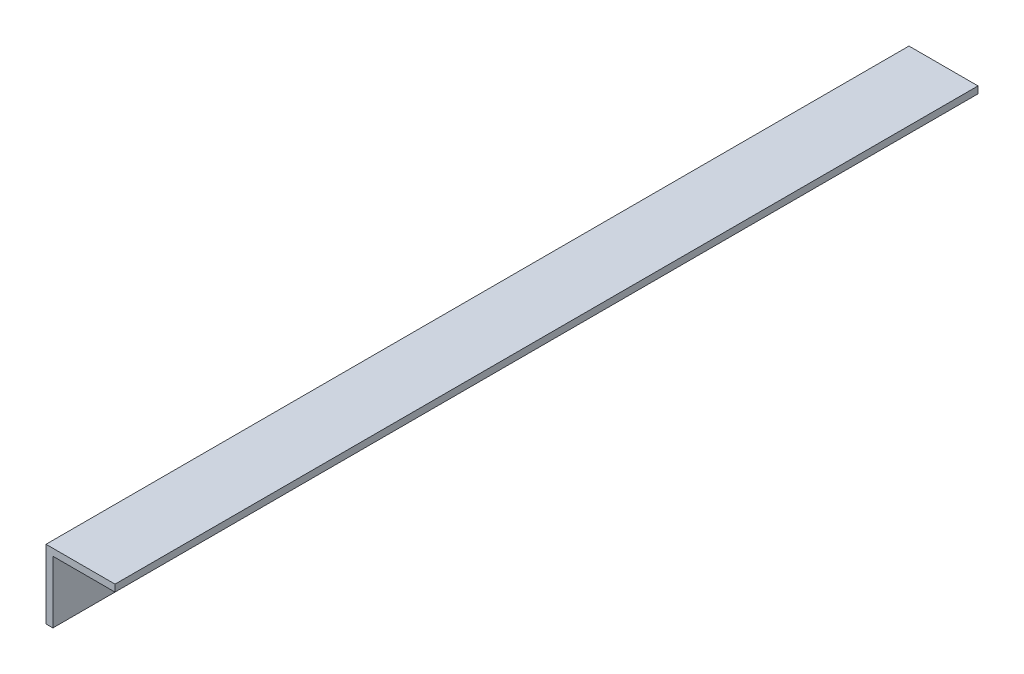
SolidWorks part; units mm, degrees
material "1.0037 (S235JR)"
ref_plane "Front Plane" through (0, 0, 0) normal (0, 0, 1) x (1, 0, 0)
ref_plane "Top Plane" through (0, 0, 0) normal (0, 1, 0) x (1, 0, 0)
ref_plane "Right Plane" through (0, 0, 0) normal (1, 0, 0) x (0, 0, -1)
sketch "Sketch1" plane through (0, 0, 0) normal (0, 0, 1) x (1, 0, 0)
  line L0 (0, 0) -> (0, 40)
  line L1 (0, 40) -> (40, 40)
  line L2 (40, 40) -> (40, 36)
  line L3 (40, 36) -> (4, 36)
  line L4 (4, 36) -> (4, 0)
  line L5 (4, 0) -> (0, 0)
  dimension "D1" = 40
  dimension "D2" = 4
extrude "Boss-Extrude1" add sketch "Sketch1" along normal blind 500
